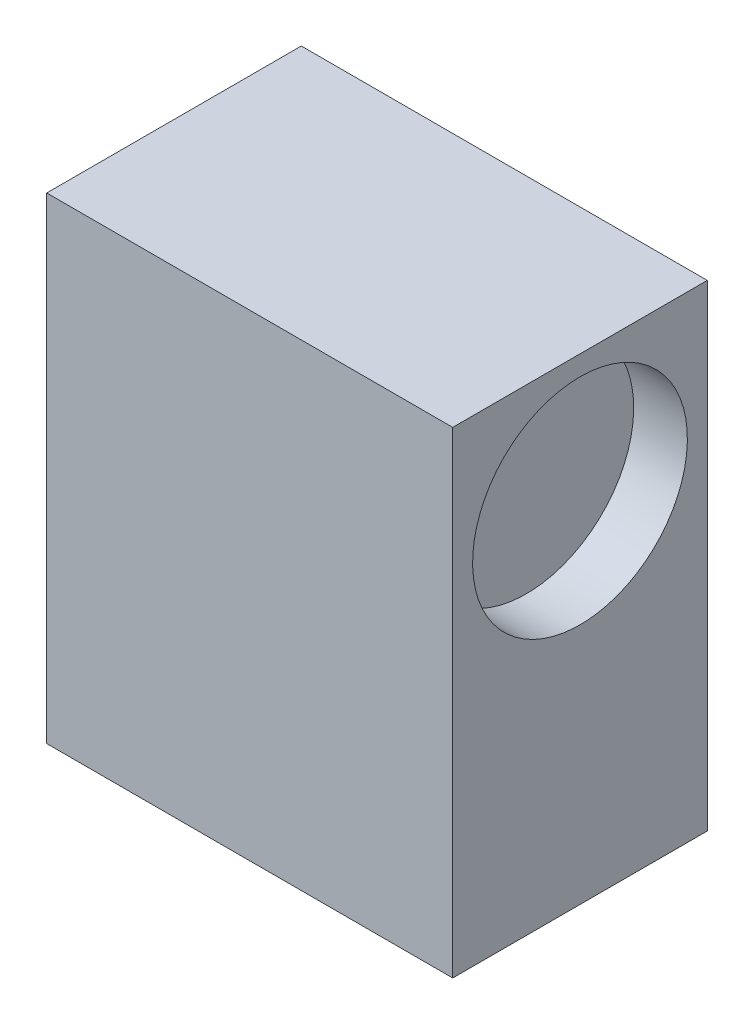
SolidWorks part; units mm, degrees
ref_plane "Front Plane" through (0, 0, 0) normal (0, 0, 1) x (1, 0, 0)
ref_plane "Top Plane" through (0, 0, 0) normal (0, 1, 0) x (1, 0, 0)
ref_plane "Right Plane" through (0, 0, 0) normal (1, 0, 0) x (0, 0, -1)
sketch "Sketch1" plane through (0, 0, 0) normal (0, 0, 1) x (1, 0, 0)
  line L1 (-3.6509, 15.2882) -> (34.1491, 15.2882)
  line L2 (-3.6509, 15.2882) -> (-3.6509, -29.1118)
  line L3 (-3.6509, -29.1118) -> (34.1491, -29.1118)
  line L4 (34.1491, 15.2882) -> (34.1491, -29.1118)
  dimension "D1" = 37.8
  dimension "D2" = 44.4
extrude "Boss-Extrude1" add sketch "Sketch1" along normal blind 23.7
sketch "Sketch2" plane through (34.1491, 0, 0) normal (1, 0, 0) x (0, 0, -1)
  circle A0 centre (-11.85, 3.4382) radius 11.85
  circle A1 centre (-11.85, 3.4382) radius 10
extrude "Cut-Extrude1" cut sketch "Sketch2" against normal blind 5 contours A1
ref_plane "Plane1" through (15.2491, 0, 0) normal (1, 0, 0) x (0, 0, -1)
mirror "Mirror1" about plane through (15.2491, 0, 0) normal (1, 0, 0) of "Cut-Extrude1"
